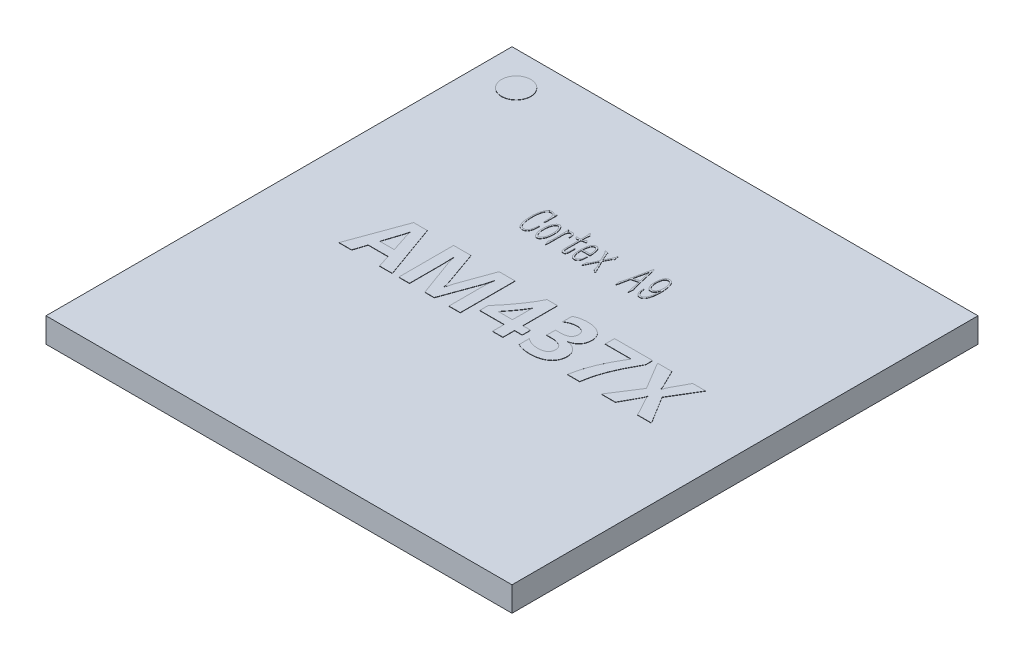
SolidWorks part; units mm, degrees
material "橡胶"
ref_plane "前视基准面" through (0, 0, 0) normal (0, 0, 1) x (1, 0, 0)
ref_plane "上视基准面" through (0, 0, 0) normal (0, 1, 0) x (1, 0, 0)
ref_plane "右视基准面" through (0, 0, 0) normal (1, 0, 0) x (0, 0, -1)
sketch "草图1" plane through (0, 0, 0) normal (0, 1, 0) x (1, 0, 0)
  line L1 (-8.5, 8.5) -> (8.5, 8.5)
  line L2 (-8.5, 8.5) -> (-8.5, -8.5)
  line L3 (-8.5, -8.5) -> (8.5, -8.5)
  line L4 (8.5, 8.5) -> (8.5, -8.5)
  line L5 (0, -8.5) -> (0, 8.5) construction
  line L6 (-8.5, 0) -> (8.5, 0) construction
  point P0 (0, 0)
  dimension "D1" = 17
  dimension "D2" = 17
extrude "凸台-拉伸1" add sketch "草图1" along normal blind 0.9
sketch "草图4" plane through (0, 0.9, 0) normal (0, 1, 0) x (1, 0, 0)
  circle A0 centre (-7.114, 7.265) radius 0.5337
extrude "凸台-拉伸3" add sketch "草图4" along normal blind 0.01
sketch "草图5" plane through (0, 0.9, 0) normal (0, 1, 0) x (1, 0, 0)
  text T0 "AM437X" font "@Microsoft YaHei UI" height 2
  text T1 "Cortex A9" font "汉仪长仿宋体" height 1.2
extrude "凸台-拉伸4" add sketch "草图5" along normal blind 0.01
